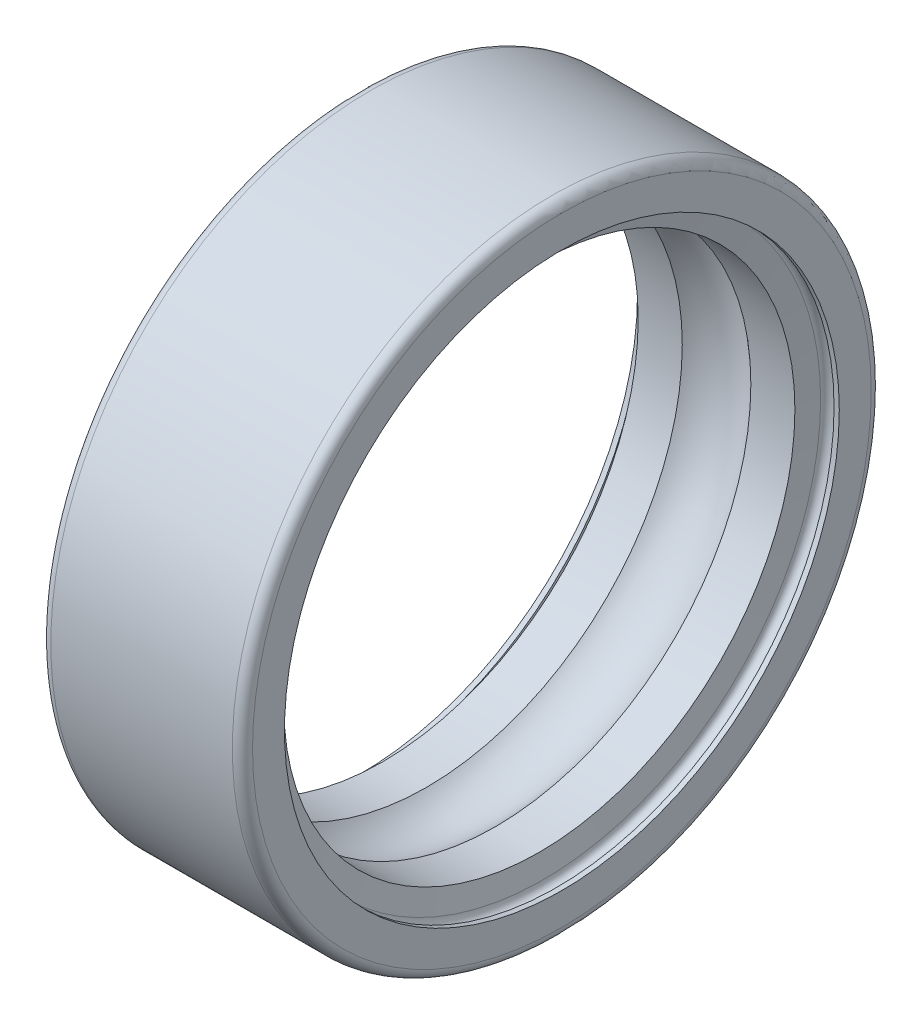
SolidWorks part; units mm, degrees
ref_plane "Front Plane" through (0, 0, 0) normal (0, 0, 1) x (1, 0, 0)
ref_plane "Top Plane" through (0, 0, 0) normal (0, 1, 0) x (1, 0, 0)
ref_plane "Right Plane" through (0, 0, 0) normal (1, 0, 0) x (0, 0, -1)
ref_plane "Plane1" through (0, 0, 0) normal (0, 0, 1) x (1, 0, 0)
sketch "Sketch1" plane through (0, 0, 0) normal (0, 0, 1) x (1, 0, 0)
  line L0 (0, 9.2) -> (0, 8.25)
  line L1 (0, 8.25) -> (0.1556, 8.25)
  line L2 (0.5556, 8.25) -> (0.6702, 7.6)
  line L3 (0.6702, 7.6) -> (1.9802, 7.6)
  line L4 (4.0198, 7.6) -> (5.3298, 7.6)
  line L5 (5.3298, 7.6) -> (5.4444, 8.25)
  line L6 (5.8444, 8.25) -> (6, 8.25)
  line L7 (6, 8.25) -> (6, 9.2)
  line L8 (5.7, 9.5) -> (0.3, 9.5)
  line L9 (5.7, 0) -> (0.3, 0) construction
  arc A0 (0.1556, 8.25) -> (0.5556, 8.25) centre (0.3556, 8.25) cw
  arc A1 (1.9802, 7.6) -> (4.0198, 7.6) centre (3, 6.5) cw
  arc A2 (5.4444, 8.25) -> (5.8444, 8.25) centre (5.6444, 8.25) cw
  arc A3 (6, 9.2) -> (5.7, 9.5) centre (5.7, 9.2) ccw
  arc A4 (0.3, 9.5) -> (0, 9.2) centre (0.3, 9.2) ccw
revolve "Revolve1" add sketch "Sketch1" angle 360 about L9
